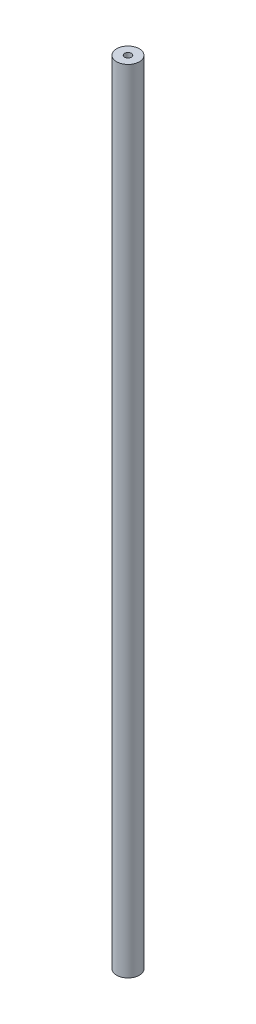
SolidWorks part; units mm, degrees
ref_plane "Front Plane" through (0, 0, 0) normal (0, 0, 1) x (1, 0, 0)
ref_plane "Top Plane" through (0, 0, 0) normal (0, 1, 0) x (1, 0, 0)
ref_plane "Right Plane" through (0, 0, 0) normal (1, 0, 0) x (0, 0, -1)
sketch "Sketch1" plane through (0, 0, 0) normal (0, 1, 0) x (1, 0, 0)
  circle A0 centre (0, 0) radius 5
  dimension "D1" = 10
extrude "Boss-Extrude1" add sketch "Sketch1" along normal blind 350 contours A0
sketch "Sketch2" plane through (0, 350, 0) normal (0, 1, 0) x (1, 0, 0)
  circle A0 centre (0, 0) radius 1.5
  dimension "D1" = 3
extrude "Cut-Extrude1" cut sketch "Sketch2" against normal blind 10
